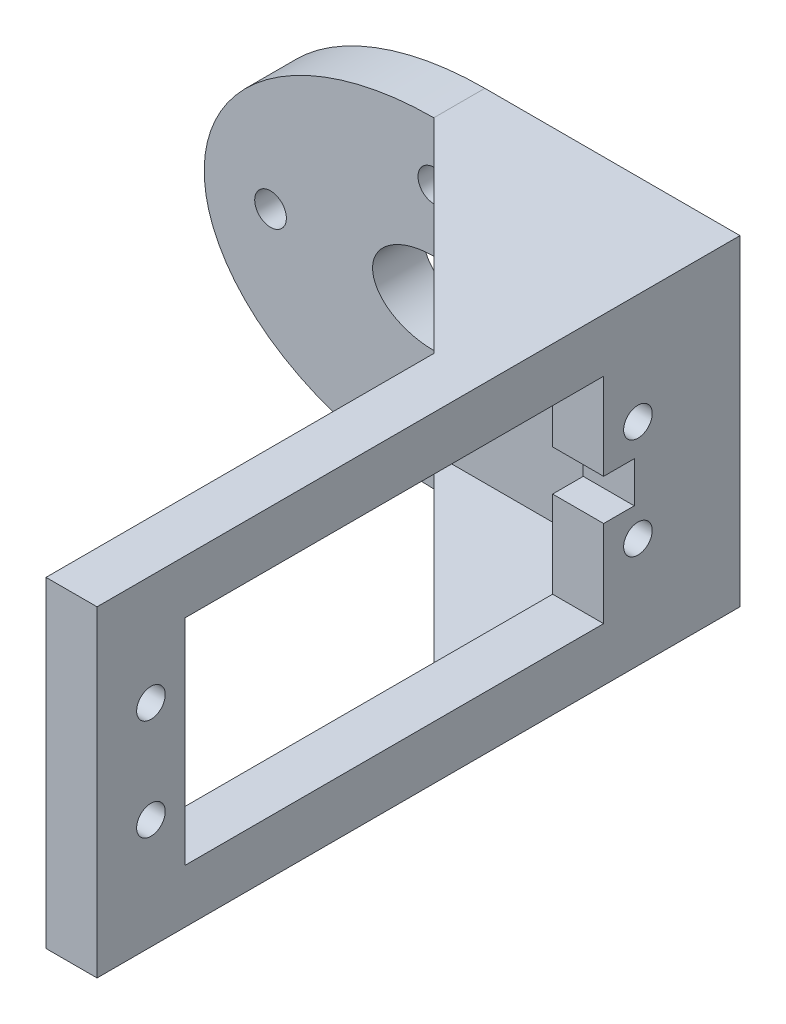
SolidWorks part; units mm, degrees
ref_plane "Plan de face" through (0, 0, 0) normal (0, 0, 1) x (1, 0, 0)
ref_plane "Plan de dessus" through (0, 0, 0) normal (0, 1, 0) x (1, 0, 0)
ref_plane "Plan de droite" through (0, 0, 0) normal (1, 0, 0) x (0, 0, -1)
sketch "Esquisse1" plane through (0, 0, 0) normal (0, 0, 1) x (1, 0, 0)
  line L0 (25, 15.75) -> (25, -15.75)
  line L1 (25, 15.75) -> (0, 15.75)
  line L2 (25, -15.75) -> (0, -15.75)
  circle A0 centre (0, -10) radius 1.55 construction
  circle A1 centre (-16, 0) radius 1.55 construction
  circle A2 centre (16, 0) radius 1.55 construction
  circle A3 centre (0, 10) radius 1.55 construction
  circle A4 centre (0, -10) radius 1.55
  circle A5 centre (-16, 0) radius 1.55
  circle A6 centre (16, 0) radius 1.55
  circle A7 centre (0, 10) radius 1.55
  ellipse E0 centre (0, 0) end of major axis (6, 0) minor radius 4 construction
  ellipse E1 centre (0, 0) end of major axis (22.5, 0) minor radius 15.75 construction
  ellipse E2 centre (0, 0) end of major axis (6, 0) minor radius 4
  ellipse E3 centre (0, 0) end of major axis (22.5, 0) minor radius 15.75
  point P36 (25, 0)
  dimension "D1" = 25
extrude "Boss.-Extru.1" add sketch "Esquisse1" along normal blind 5 contours E3 L0 L1 | L0 E3 A4 A5 A6 A7 E2 | E3 L2 L0 | L0 E3
sketch "Esquisse3" plane through (0, 0, 5) normal (0, 0, 1) x (1, 0, 0)
  line L0 (25, -15.75) -> (0, -15.75) construction
  line L1 (25, 15.75) -> (20, 15.75)
  line L2 (25, 15.75) -> (25, -15.75)
  line L3 (25, -15.75) -> (20, -15.75)
  line L4 (20, 15.75) -> (20, -15.75)
  dimension "D1" = 5
extrude "Boss.-Extru.2" add sketch "Esquisse3" along normal blind 58
sketch "Esquisse4" plane through (20, 0, 0) normal (-1, 0, 0) x (0, 0, 1)
  line L0 (5, -15.75) -> (5, 15.75) construction
  circle A0 centre (10, 4.96) radius 1.4
  circle A1 centre (10, -4.96) radius 1.4
  circle A2 centre (57.72, -4.96) radius 1.4
  circle A3 centre (57.72, 4.96) radius 1.4
  point P8 (0, 0)
  point P9 (0, 0)
  point P10 (0, 0)
  point P11 (10.268, 5.563)
  point P12 (0, 0)
  dimension "D1" = 2.8
  dimension "D2" = 9.92
  dimension "D3" = 47.72
  dimension "D4" = 4.96
  dimension "D5" = 5
extrude "Enlèv. mat.-Extru.1" cut sketch "Esquisse4" against normal blind 5
sketch "Esquisse5" plane through (0, 15.75, 0) normal (0, 1, 0) x (1, 0, 0)
  line L0 (0, -5) -> (20, -5)
  line L1 (20, -5) -> (0, -5) construction
  line L2 (20, -5) -> (20, -25)
  line L3 (20, -63) -> (20, -5) construction
  line L4 (20, -25) -> (0, -5)
  dimension "D1" = 20
  dimension "D2" = 20
extrude "Boss.-Extru.3" add sketch "Esquisse5" against normal blind 3
mirror "Symétrie1" about plane through (0, 0, 0) normal (0, 1, 0) of "Boss.-Extru.3"
sketch "Esquisse6" plane through (20, 0, 0) normal (-1, 0, 0) x (0, 0, 1)
  line L0 (10, 4.96) -> (57.72, -4.96) construction
  line L1 (57.72, 4.96) -> (10, -4.96) construction
  line L3 (13.36, -10.5) -> (54.36, -10.5)
  line L4 (13.36, -10.5) -> (13.36, 10.5)
  line L5 (13.36, 10.5) -> (54.36, 10.5)
  line L6 (54.36, -10.5) -> (54.36, 10.5)
  line L7 (13.36, -10.5) -> (54.36, 10.5) construction
  line L8 (13.36, 10.5) -> (54.36, -10.5) construction
  line L9 (13.36, 2) -> (10.36, 2)
  line L10 (13.36, 2) -> (13.36, -2)
  line L11 (13.36, -2) -> (10.36, -2)
  line L12 (10.36, 2) -> (10.36, -2)
  point P7 (33.86, 0)
  point P16 (10.36, 0)
  point P17 (10.36, -1.9955)
  dimension "D1" = 41
  dimension "D2" = 21
  dimension "D3" = 3
  dimension "D4" = 4
extrude "Enlèv. mat.-Extru.2" cut sketch "Esquisse6" against normal blind 5 contours L9 L12 L11 L4 | L3 L6 L5 L4
